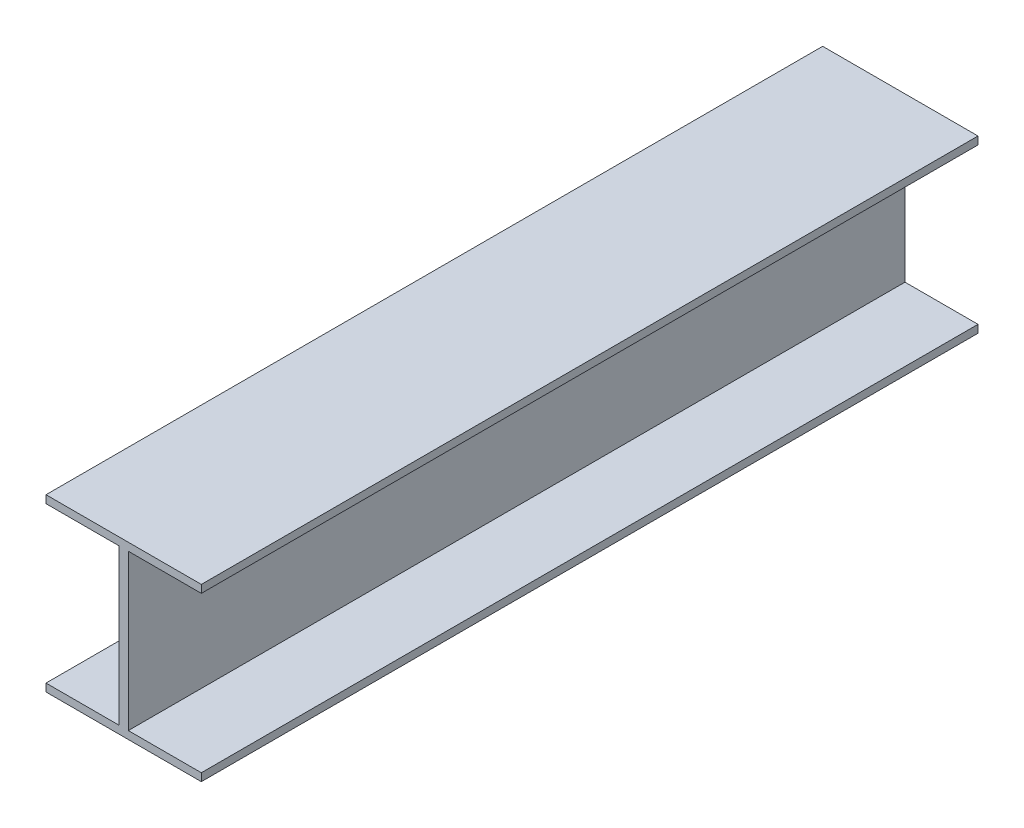
SolidWorks part; units mm, degrees
material "1.0037 (S235JR)"
ref_plane "Front Plane" through (0, 0, 0) normal (0, 0, 1) x (1, 0, 0)
ref_plane "Top Plane" through (0, 0, 0) normal (0, 1, 0) x (1, 0, 0)
ref_plane "Right Plane" through (0, 0, 0) normal (1, 0, 0) x (0, 0, -1)
sketch "Sketch1" plane through (0, 0, 0) normal (0, 0, 1) x (1, 0, 0)
  line L0 (-3, 0) -> (3, 0) construction
  line L2 (3, -50) -> (3, 50)
  line L4 (-3, -50) -> (-3, 50)
  line L5 (-50, 55) -> (50, 50) construction
  line L6 (-50, -50) -> (50, -55) construction
  line L7 (-50, 50) -> (-3, 50)
  line L8 (-50, 50) -> (-50, 55)
  line L9 (-50, 55) -> (50, 55)
  line L10 (50, 50) -> (50, 55)
  line L11 (0, -52.5) -> (0, 52.5) construction
  line L12 (3, 50) -> (50, 50)
  line L13 (-50, -55) -> (50, -55)
  line L14 (50, -50) -> (50, -55)
  line L15 (-50, -50) -> (-3, -50)
  line L16 (-50, -50) -> (-50, -55)
  line L17 (3, -50) -> (50, -50)
  point P0 (0, 0)
  dimension "D1" = 100
  dimension "D2" = 5
  dimension "D3" = 100
  dimension "D4" = 6
extrude "Boss-Extrude1" add sketch "Sketch1" along normal blind 500
